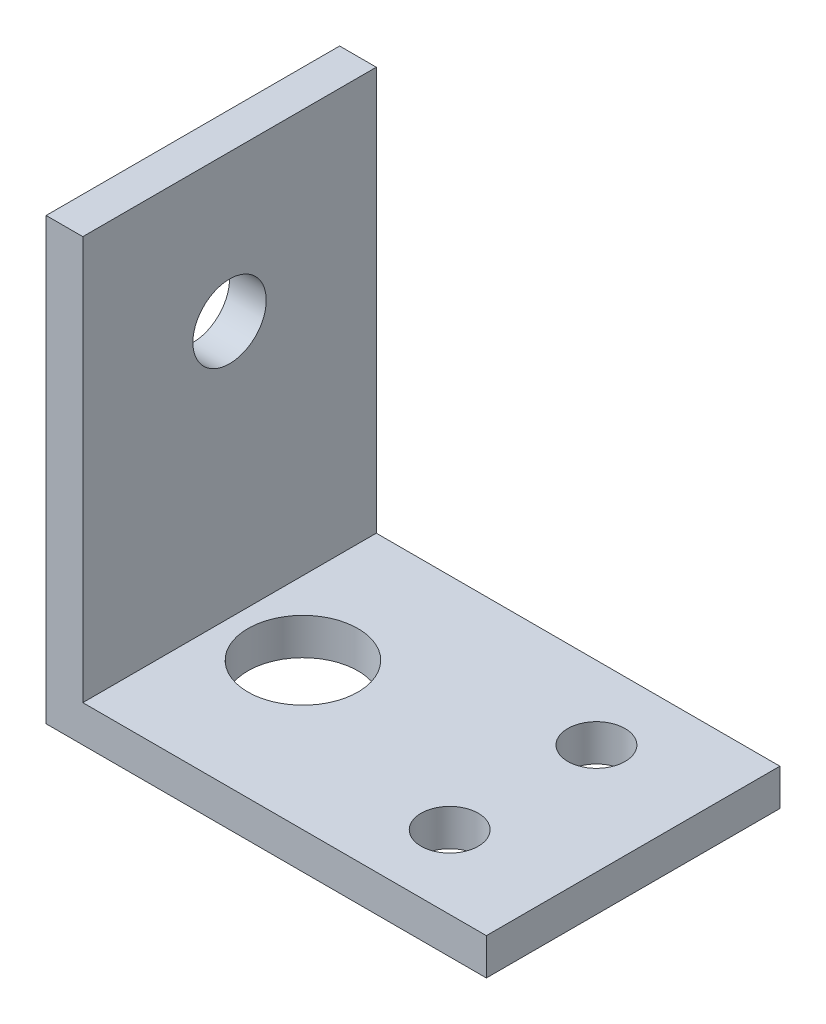
SolidWorks part; units mm, degrees
ref_plane "Front Plane" through (0, 0, 0) normal (0, 0, 1) x (1, 0, 0)
ref_plane "Top Plane" through (0, 0, 0) normal (0, 1, 0) x (1, 0, 0)
ref_plane "Right Plane" through (0, 0, 0) normal (1, 0, 0) x (0, 0, -1)
sketch "Sketch1" plane through (0, 0, 0) normal (0, 0, 1) x (1, 0, 0)
  line L0 (0, 0) -> (38.1, 0)
  line L1 (0, 0) -> (0, 38.1)
  dimension "D1" = 38.1
extrude "Extrude-Thin1" add sketch "Sketch1" along normal blind 25.4 thin thin type one direction wall 3.175
sketch "Sketch2" plane through (0, 3.175, 0) normal (0, 1, 0) x (1, 0, 0)
  line L0 (0, -25.4) -> (0, 0) construction
  circle A0 centre (9.525, -12.7) radius 4.7625
  point P5 (0, -12.7)
  dimension "D1" = 9.525
  dimension "D2" = 9.525
extrude "Cut-Extrude1" cut sketch "Sketch2" against normal through all
sketch "Sketch3" plane through (0, 0, 0) normal (0, -1, 0) x (1, 0, 0)
  line L0 (28.575, 25.4) -> (28.575, 0) construction
  line L1 (38.1, 25.4) -> (0, 25.4) construction
  line L2 (38.1, 0) -> (0, 0) construction
  line L3 (28.575, 19.05) -> (28.575, 6.35) construction
  line L4 (38.1, 25.4) -> (38.1, 0) construction
  circle A0 centre (28.575, 19.05) radius 2.4765
  circle A1 centre (28.575, 6.35) radius 2.4765
  point P9 (28.575, 12.7)
  dimension "D1" = 4.953
  dimension "D2" = 12.7
  dimension "D3" = 9.525
extrude "Cut-Extrude2" cut sketch "Sketch3" against normal through all
sketch "Sketch4" plane through (0, 0, 0) normal (-1, 0, 0) x (0, 0, 1)
  line L0 (25.4, 0) -> (0, 0) construction
  line L1 (12.7, 0) -> (12.7, 38.1) construction
  line L2 (25.4, 38.1) -> (0, 38.1) construction
  circle A0 centre (12.7, 25.4) radius 3.175
  dimension "D2" = 6.35
  dimension "D1" = 25.4
extrude "Cut-Extrude3" cut sketch "Sketch4" against normal through all
